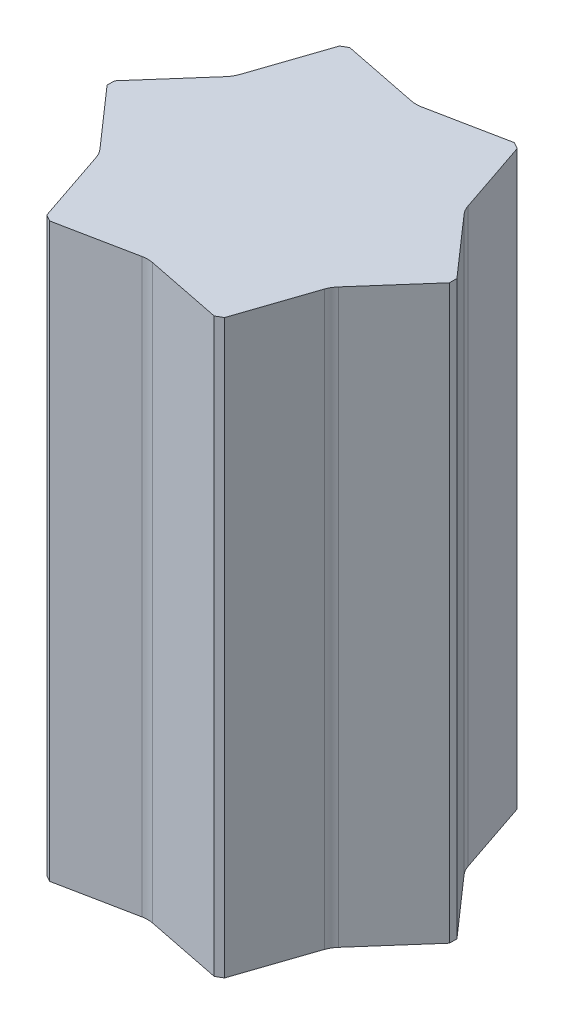
SolidWorks part; units mm, degrees
material "PEN"
ref_plane "前视基准面" through (0, 0, 0) normal (0, 0, 1) x (1, 0, 0)
ref_plane "上视基准面" through (0, 0, 0) normal (0, 1, 0) x (1, 0, 0)
ref_plane "右视基准面" through (0, 0, 0) normal (1, 0, 0) x (0, 0, -1)
sketch "草图1" plane through (0, 0, 0) normal (0, 1, 0) x (1, 0, 0)
  line L1 (395, 8.6603) -> (205, 337.7499)
  line L2 (190, 346.4102) -> (-190, 346.4102)
  line L3 (-205, 337.7499) -> (-395, 8.6603)
  line L4 (-395, -8.6603) -> (-205, -337.7499)
  line L5 (-190, -346.4102) -> (190, -346.4102)
  line L6 (205, -337.7499) -> (395, -8.6603)
  line L8 (190, 346.4102) -> (205, 337.7499)
  line L10 (395, -8.6603) -> (395, 8.6603)
  line L12 (205, -337.7499) -> (190, -346.4102)
  line L14 (-395, 8.6603) -> (-395, -8.6603)
  line L18 (-190, 346.4102) -> (-205, 337.7499)
  line L20 (-190, -346.4102) -> (-205, -337.7499)
extrude "凸台-拉伸1" add sketch "草图1" along normal mid plane 1320
sketch "草图4" plane through (0, 0, 0) normal (0, 1, 0) x (1, 0, 0)
  line L1 (190, 369.6203) -> (190, 346.4102)
  line L2 (11.76, 310.7841) -> (190, 346.4102)
  line L3 (-190, 346.4102) -> (-11.76, 310.7841)
  line L4 (-190, 369.6203) -> (-190, 346.4102)
  line L6 (-190, 369.6203) -> (-190, 392.8305)
  line L8 (-11.76, 428.4566) -> (-190, 392.8305)
  line L9 (190, 392.8305) -> (11.76, 428.4566)
  line L10 (190, 369.6203) -> (190, 392.8305)
  line L11 (415.1006, 20.2653) -> (395, 8.6603)
  line L17 (275.0269, 145.2076) -> (395, 8.6603)
  line L18 (205, 337.7499) -> (263.2669, 165.5765)
  line L19 (225.1006, 349.355) -> (205, 337.7499)
  line L20 (225.1006, 349.355) -> (245.2012, 360.9601)
  line L21 (365.1743, 224.4127) -> (245.2012, 360.9601)
  line L22 (435.2012, 31.8704) -> (376.9343, 204.0438)
  line L23 (415.1006, 20.2653) -> (435.2012, 31.8704)
  line L24 (225.1006, -349.355) -> (205, -337.7499)
  line L25 (263.2669, -165.5765) -> (205, -337.7499)
  line L26 (395, -8.6603) -> (275.0269, -145.2076)
  line L27 (415.1006, -20.2653) -> (395, -8.6603)
  line L28 (415.1006, -20.2653) -> (435.2012, -31.8704)
  line L29 (376.9343, -204.0438) -> (435.2012, -31.8704)
  line L30 (245.2012, -360.9601) -> (365.1743, -224.4127)
  line L31 (225.1006, -349.355) -> (245.2012, -360.9601)
  line L32 (-190, -369.6203) -> (-190, -346.4102)
  line L33 (-11.76, -310.7841) -> (-190, -346.4102)
  line L34 (190, -346.4102) -> (11.76, -310.7841)
  line L35 (190, -369.6203) -> (190, -346.4102)
  line L36 (190, -369.6203) -> (190, -392.8305)
  line L37 (11.76, -428.4566) -> (190, -392.8305)
  line L38 (-190, -392.8305) -> (-11.76, -428.4566)
  line L39 (-190, -369.6203) -> (-190, -392.8305)
  line L40 (-415.1006, -20.2653) -> (-395, -8.6603)
  line L41 (-275.0269, -145.2076) -> (-395, -8.6603)
  line L42 (-205, -337.7499) -> (-263.2669, -165.5765)
  line L43 (-225.1006, -349.355) -> (-205, -337.7499)
  line L44 (-225.1006, -349.355) -> (-245.2012, -360.9601)
  line L45 (-365.1743, -224.4127) -> (-245.2012, -360.9601)
  line L46 (-435.2012, -31.8704) -> (-376.9343, -204.0438)
  line L47 (-415.1006, -20.2653) -> (-435.2012, -31.8704)
  line L48 (-225.1006, 349.355) -> (-205, 337.7499)
  line L49 (-263.2669, 165.5765) -> (-205, 337.7499)
  line L50 (-395, 8.6603) -> (-275.0269, 145.2076)
  line L51 (-415.1006, 20.2653) -> (-395, 8.6603)
  line L52 (-415.1006, 20.2653) -> (-435.2012, 31.8704)
  line L53 (-376.9343, 204.0438) -> (-435.2012, 31.8704)
  line L54 (-245.2012, 360.9601) -> (-365.1743, 224.4127)
  line L55 (-225.1006, 349.355) -> (-245.2012, 360.9601)
  arc A0 (-11.76, 310.7841) -> (11.76, 310.7841) centre (0, 369.6203) ccw
  arc A1 (11.76, 428.4566) -> (-11.76, 428.4566) centre (0, 369.6203) ccw
  arc A2 (263.2669, 165.5765) -> (275.0269, 145.2076) centre (320.1006, 184.8102) ccw
  arc A3 (376.9343, 204.0438) -> (365.1743, 224.4127) centre (320.1006, 184.8102) ccw
  arc A4 (275.0269, -145.2076) -> (263.2669, -165.5765) centre (320.1006, -184.8102) ccw
  arc A5 (365.1743, -224.4127) -> (376.9343, -204.0438) centre (320.1006, -184.8102) ccw
  arc A8 (11.76, -310.7841) -> (-11.76, -310.7841) centre (0, -369.6203) ccw
  arc A9 (-11.76, -428.4566) -> (11.76, -428.4566) centre (0, -369.6203) ccw
  arc A10 (-263.2669, -165.5765) -> (-275.0269, -145.2076) centre (-320.1006, -184.8102) ccw
  arc A11 (-376.9343, -204.0438) -> (-365.1743, -224.4127) centre (-320.1006, -184.8102) ccw
  arc A12 (-275.0269, 145.2076) -> (-263.2669, 165.5765) centre (-320.1006, 184.8102) ccw
  arc A13 (-365.1743, 224.4127) -> (-376.9343, 204.0438) centre (-320.1006, 184.8102) ccw
  dimension "D1" = 6
extrude "切除-拉伸1" cut sketch "草图4" against normal through all both and the other way through all
sketch "草图5" plane through (0, 0, 0) normal (0, 0, 1) x (1, 0, 0)
  line L0 (0, -660) -> (0, 660)
  line L1 (-11.76, -660) -> (11.76, -660) construction
  line L2 (11.76, 660) -> (-11.76, 660) construction
